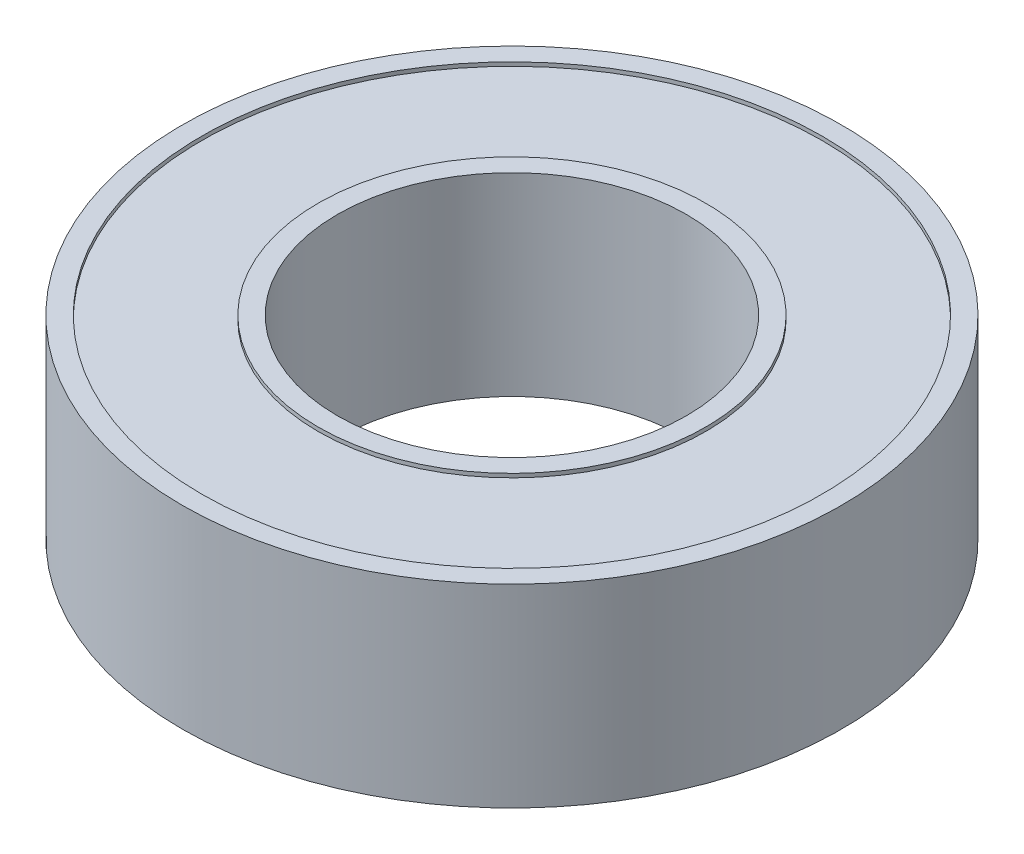
SolidWorks part; units mm, degrees
material "1060-H16"
ref_plane "Front Plane" through (0, 0, 0) normal (0, 0, 1) x (1, 0, 0)
ref_plane "Top Plane" through (0, 0, 0) normal (0, 1, 0) x (1, 0, 0)
ref_plane "Right Plane" through (0, 0, 0) normal (1, 0, 0) x (0, 0, -1)
sketch "Sketch1" plane through (0, 0, 0) normal (0, 1, 0) x (1, 0, 0)
  circle A0 centre (0, 0) radius 4.5
  circle A1 centre (0, 0) radius 8.5
  dimension "D1" = 9
  dimension "D2" = 17
extrude "Boss-Extrude1" add sketch "Sketch1" along normal mid plane 5
sketch "Sketch2" plane through (0, 2.5, 0) normal (0, 1, 0) x (1, 0, 0)
  circle A0 centre (0, 0) radius 4.5 construction
  circle A1 centre (0, 0) radius 8.5
  circle A2 centre (0, 0) radius 8.5
  circle A3 centre (0, 0) radius 4.5
  circle A5 centre (0, 0) radius 5
  circle A8 centre (0, 0) radius 8
  dimension "D1" = 0
  dimension "D2" = 0.5
  dimension "D3" = 0.5
extrude "Cut-Extrude1" cut sketch "Sketch2" against normal blind 0.1 contours A8 A5
mirror "Mirror1" about plane through (0, 0, 0) normal (0, 1, 0) of "Cut-Extrude1"
